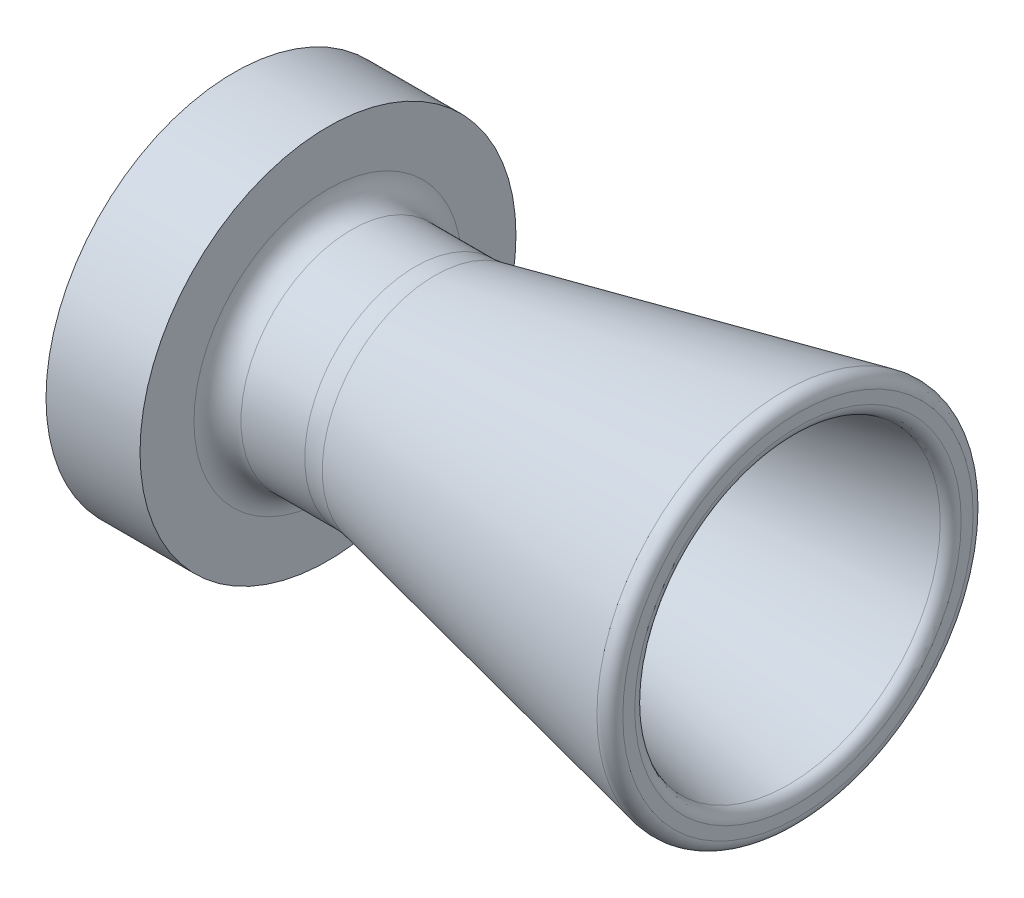
SolidWorks part; units mm, degrees
ref_plane "Front Plane" through (0, 0, 0) normal (0, 0, 1) x (1, 0, 0)
ref_plane "Top Plane" through (0, 0, 0) normal (0, 1, 0) x (1, 0, 0)
ref_plane "Right Plane" through (0, 0, 0) normal (1, 0, 0) x (0, 0, -1)
ref_axis "Axis1" through (88.99, 0, 0) along (-1, 0, 0)
sketch "Sketch1" plane through (0, 0, 0) normal (0, 1, 0) x (1, 0, 0)
  line L0 (88.99, 0) -> (-88.99, 0) construction
  line L1 (-1.9329, -25.2304) -> (-49.0625, -15.2127)
  line L2 (-76.2, -9.525) -> (-63.5, -9.525)
  line L3 (-63.5, -10.16) -> (-51.2011, -10.16)
  line L4 (0, -22.0552) -> (0, -23.6652)
  line L5 (-50.3682, -10.0533) -> (-50.3682, -10.1873)
  line L6 (-63.5, -9.525) -> (-63.5, -10.16)
  line L7 (-76.2, -9.525) -> (-76.2, -25.4)
  line L8 (-76.2, -25.4) -> (-63.5, -25.4)
  line L9 (-1.2675, -20.49) -> (-48.5607, -10.4375)
  line L10 (0, -20.7594) -> (-50.3682, -10.0533) construction
  line L11 (0, 0.1067) -> (0, -76.0933) construction
  line L12 (-50.3682, 0.1067) -> (-50.3682, -76.0933) construction
  line L13 (-63.5, 0.1067) -> (-63.5, -76.0933) construction
  line L14 (-76.2, 0.1067) -> (-76.2, -76.0933) construction
  line L19 (-0.9928, -25.4303) -> (-51.361, -14.7242) construction
  line L20 (-51.703, -14.9352) -> (-60.325, -14.9352)
  line L21 (-63.5, -18.1102) -> (-63.5, -25.4)
  arc A0 (0, -22.0552) -> (-1.2675, -20.49) centre (-1.6002, -22.0552) ccw
  arc A1 (-1.9329, -25.2304) -> (0, -23.6652) centre (-1.6002, -23.6652) ccw
  arc A2 (-51.703, -14.9352) -> (-49.0625, -15.2127) centre (-51.703, -27.6352) cw
  arc A3 (-51.2011, -10.16) -> (-48.5607, -10.4375) centre (-51.2011, -22.86) cw
  arc A4 (-63.5, -18.1102) -> (-60.325, -14.9352) centre (-60.325, -18.1102) cw
  point P0 (-108.7705, 0)
  point P5 (-108.7705, -9.525)
  point P6 (0, -9.525)
  point P7 (-108.7705, -10.16)
  point P8 (0, -10.16)
  point P16 (-108.7705, -25.4)
  point P17 (0, -25.4)
  point P18 (-50.3682, -10.16)
  point P36 (-50.3682, -14.9352)
  dimension "D8" = 1.6002
  dimension "D9" = 1.6002
  dimension "D10" = 12.7
  dimension "D11" = 12.7
  dimension "D12" = 3.175
  dimension "D4" = 63.5
  dimension "D7" = 4.7752
  dimension "D2" = 4.7752
  dimension "D6" = 25.4
  dimension "D13" = 10.16
  dimension "D14" = 9.525
  dimension "D3" = 50.3682
  dimension "D5" = 76.2
revolve "Revolve3" add sketch "Sketch1" angle 360 about axis through (88.99, 0, 0) along (-1, 0, 0)
